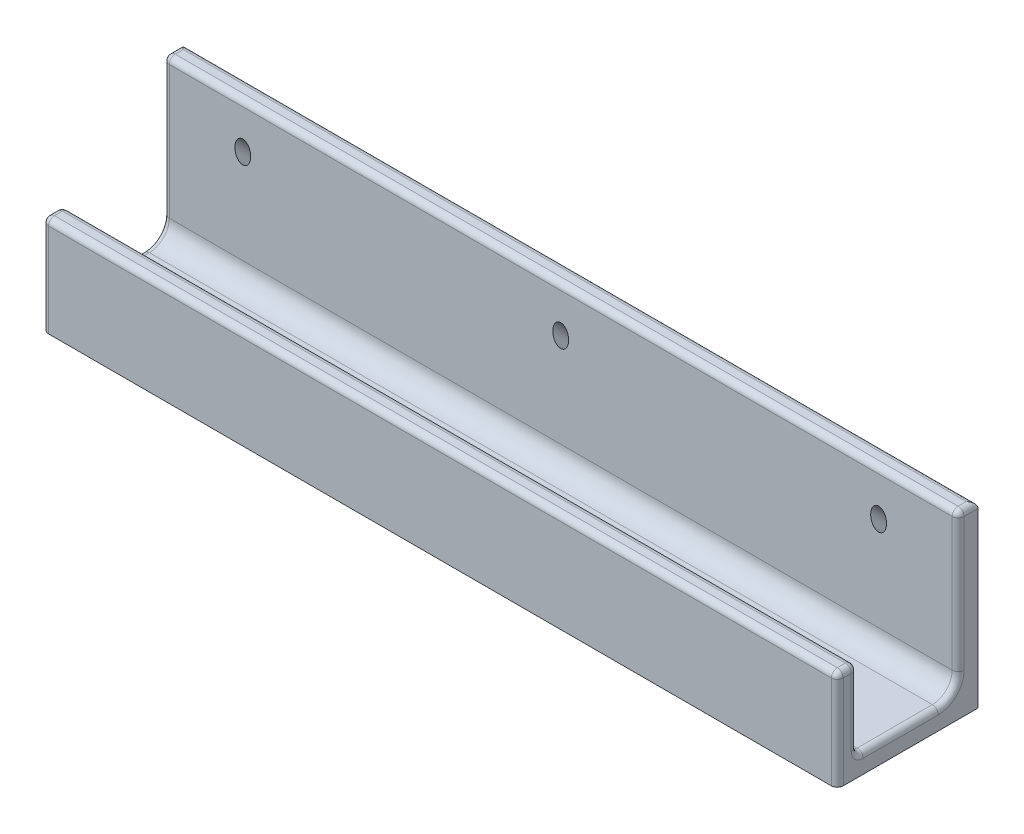
SolidWorks part; units mm, degrees
ref_plane "Front Plane" through (0, 0, 0) normal (0, 0, 1) x (1, 0, 0)
ref_plane "Top Plane" through (0, 0, 0) normal (0, 1, 0) x (1, 0, 0)
ref_plane "Right Plane" through (0, 0, 0) normal (1, 0, 0) x (0, 0, -1)
sketch "Sketch1" plane through (0, 0, 0) normal (1, 0, 0) x (0, 0, -1)
  line L0 (0, 0) -> (-12.7, 0)
  line L1 (-12.7, 0) -> (-12.7, 20)
  line L2 (0, 0) -> (12.7, 0)
  line L3 (12.7, 0) -> (12.7, 40)
  dimension "D1" = 25.4
  dimension "D2" = 20
  dimension "D3" = 40
extrude "Extrude-Thin1" add sketch "Sketch1" along normal mid plane 200 thin thin type one direction wall 5
ref_plane "Plane1" through (0, 13.65, 13.65) normal (0, 0.7071, 0.7071) x (-1, 0, 0)
sketch "Sketch2" plane through (0, 13.65, 13.65) normal (0, 0.7071, 0.7071) x (-1, 0, 0)
  line L0 (-100, -37.2645) -> (100, -37.2645) construction
  line L1 (0, 0) -> (0, -29.2645) construction
  point P0 (80, -29.2645)
  point P11 (-80, -29.2645)
  point P14 (0, -29.2645)
  point P16 (0, 0)
  dimension "D1" = 8
  dimension "D2" = 80
hole_wizard "Ø4.0 (4) Diameter Hole1" positions "Sketch2" profile "Sketch3" hole size "Ø4.0" standard "ANSI Metric"
sketch "Sketch3" plane through (-80, 34.3431, -7.0431) normal (1, 0, 0) x (0, -0.7071, 0.7071)
  line L0 (0, 0) -> (0, 15.0711)
  line L1 (0, 15.0711) -> (2, 15.0711)
  line L2 (2, 15.0711) -> (2, 0)
  line L5 (2, 0) -> (0, 0)
  line L11 (0, -6.35) -> (0, 107.95) construction
  dimension "Thru Hole Dia." = 4
  dimension "Thru Hole Depth" = 15.0711
fillet "Fillet3" radius 5 1 edges at (0, 0, -12.7)
fillet "Fillet2" radius 1.5 19 edges at (-100, 22.5, -12.7) (0, 0, 12.7) (-100, 0, 2.5) (-100, 10, 12.7) (100, 10, 12.7) (100, 0, 2.5) (100, 22.5, -12.7) (0, 20, 12.7) (100, 20, 15.2) (0, 20, 17.7) (-100, 20, 15.2) (0, 40, -17.7) (100, 40, -15.2) (0, 40, -12.7) (-100, 40, -15.2) (100, 7.5, 17.7) (-100, 7.5, 17.7) (-100, 1.4645, -11.2355) (100, 1.4645, -11.2355)
